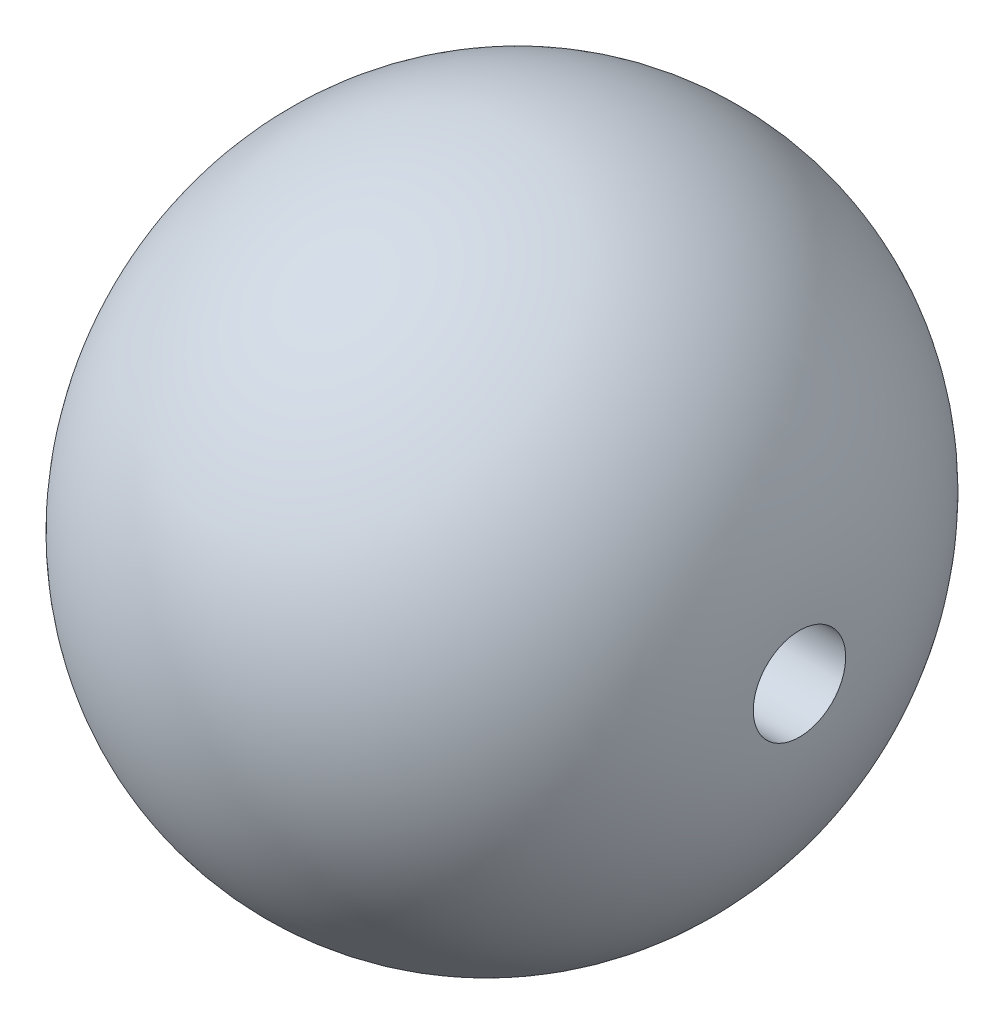
SolidWorks part; units mm, degrees
ref_plane "Front Plane" through (0, 0, 0) normal (0, 0, 1) x (1, 0, 0)
ref_plane "Top Plane" through (0, 0, 0) normal (0, 1, 0) x (1, 0, 0)
ref_plane "Right Plane" through (0, 0, 0) normal (1, 0, 0) x (0, 0, -1)
sketch "Sketch1" plane through (0, 0, 0) normal (0, 1, 0) x (1, 0, 0)
  line L0 (0, 0) -> (16, 0)
  line L1 (0, 0) -> (0, 18)
  arc A0 (0, 18) -> (16, 0) centre (0, 1.8889) cw
  dimension "D1" = 18
  dimension "D2" = 16
revolve "Revolve1" add sketch "Sketch1" angle 360 about L0
mirror "Mirror2" about plane through (0, 0, 0) normal (1, 0, 0) of "Revolve1"
sketch "Sketch2" plane through (0, 0, 0) normal (1, 0, 0) x (0, 0, -1)
  circle A0 centre (0, 0) radius 2.5
  dimension "D1" = 5
extrude "Cut-Extrude1" cut sketch "Sketch2" against normal blind 26 and the other way blind 27
